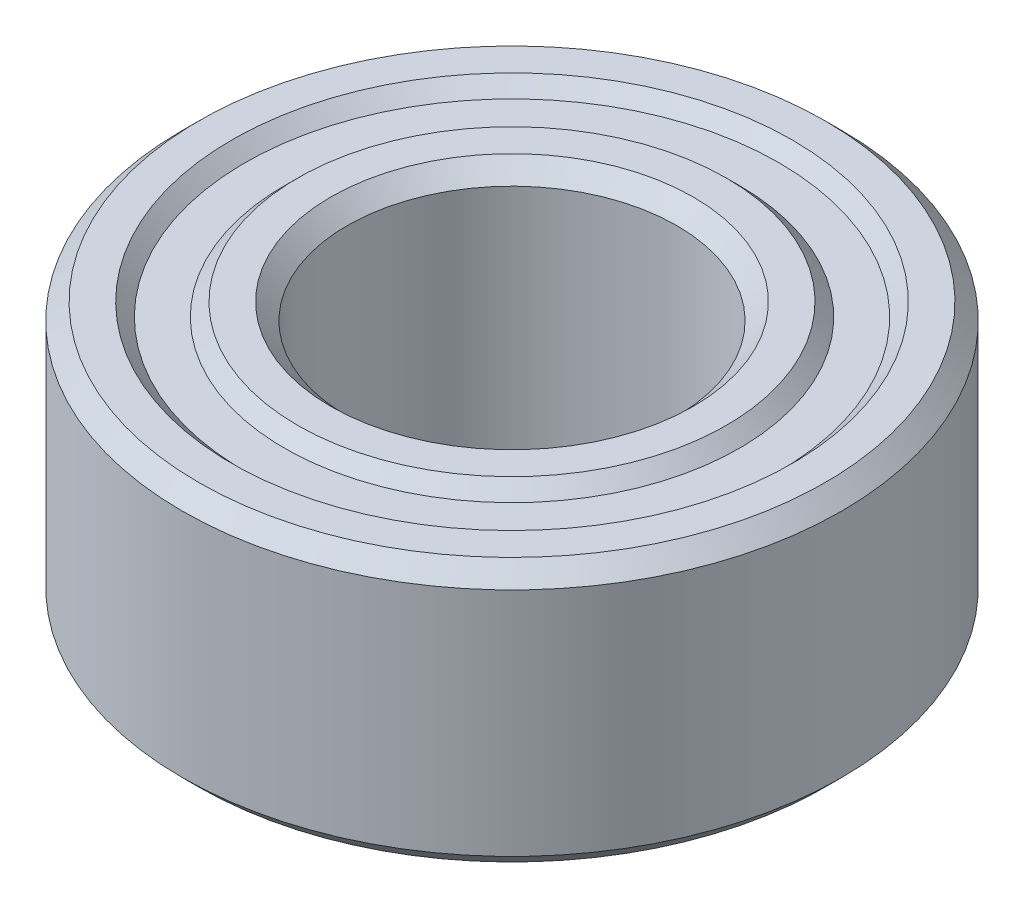
SolidWorks part; units mm, degrees
material "Stainless Steel (ferritic)"
ref_plane "Front Plane" through (0, 0, 0) normal (0, 0, 1) x (1, 0, 0)
ref_plane "Top Plane" through (0, 0, 0) normal (0, 1, 0) x (1, 0, 0)
ref_plane "Right Plane" through (0, 0, 0) normal (1, 0, 0) x (0, 0, -1)
sketch "Sketch1" plane through (0, 0, 0) normal (0, 0, 1) x (1, 0, 0)
  line L0 (0, -1.3494) -> (0, 70.5256) construction
  line L1 (2.5, 1.75) -> (2.5, -1.75)
  line L2 (2.5, -1.75) -> (2.75, -2)
  line L3 (2.75, -2) -> (3.25, -2)
  line L4 (3.25, -2) -> (3.45, -1.8)
  line L5 (3.45, -1.8) -> (4.05, -1.8)
  line L6 (4.05, -1.8) -> (4.25, -2)
  line L7 (4.25, -2) -> (4.75, -2)
  line L8 (4.75, -2) -> (5, -1.75)
  line L9 (5, -1.75) -> (5, 1.75)
  line L10 (5, 1.75) -> (4.75, 2)
  line L11 (4.75, 2) -> (4.25, 2)
  line L12 (4.25, 2) -> (4.05, 1.8)
  line L13 (4.05, 1.8) -> (3.45, 1.8)
  line L14 (3.45, 1.8) -> (3.25, 2)
  line L15 (3.25, 2) -> (2.75, 2)
  line L16 (2.75, 2) -> (2.5, 1.75)
  line L17 (0, 0) -> (2.5, 0) construction
  dimension "D1" = 2.5
  dimension "D2" = 4
  dimension "D3" = 0.25
  dimension "D4" = 0.2
  dimension "D5" = 5
  dimension "D6" = 0.5
revolve "Revolve1" add sketch "Sketch1" angle 360 about L0
